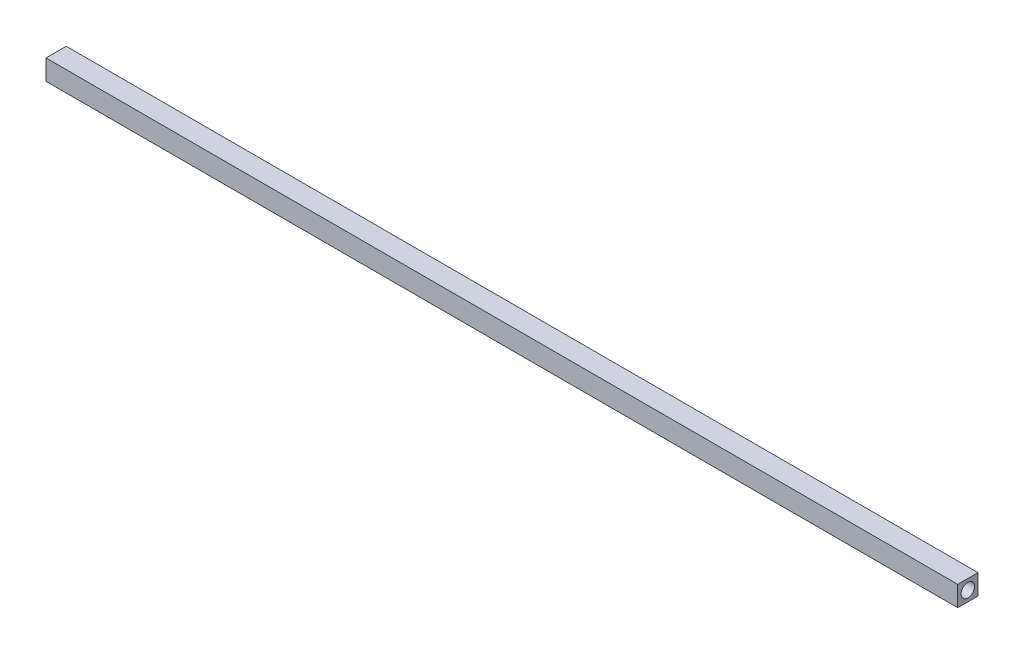
SolidWorks part; units mm, degrees
ref_plane "前视基准面" through (0, 0, 0) normal (0, 0, 1) x (1, 0, 0)
ref_plane "上视基准面" through (0, 0, 0) normal (0, 1, 0) x (1, 0, 0)
ref_plane "右视基准面" through (0, 0, 0) normal (1, 0, 0) x (0, 0, -1)
other "Configuration Table"
sketch "草图1" plane through (0, 0, 0) normal (1, 0, 0) x (0, 0, -1)
  line L1 (-1.5, 1.5) -> (1.5, 1.5)
  line L2 (-1.5, 1.5) -> (-1.5, -1.5)
  line L3 (-1.5, -1.5) -> (1.5, -1.5)
  line L4 (1.5, 1.5) -> (1.5, -1.5)
  line L5 (-1.5, 1.5) -> (1.5, -1.5) construction
  line L6 (-1.5, -1.5) -> (1.5, 1.5) construction
  circle A0 centre (0, 0) radius 1
  point P0 (0, 0)
  dimension "D3" = 2
  dimension "D1" = 3
  dimension "D2" = 3
extrude "凸台-拉伸1" add sketch "草图1" along normal blind 135
